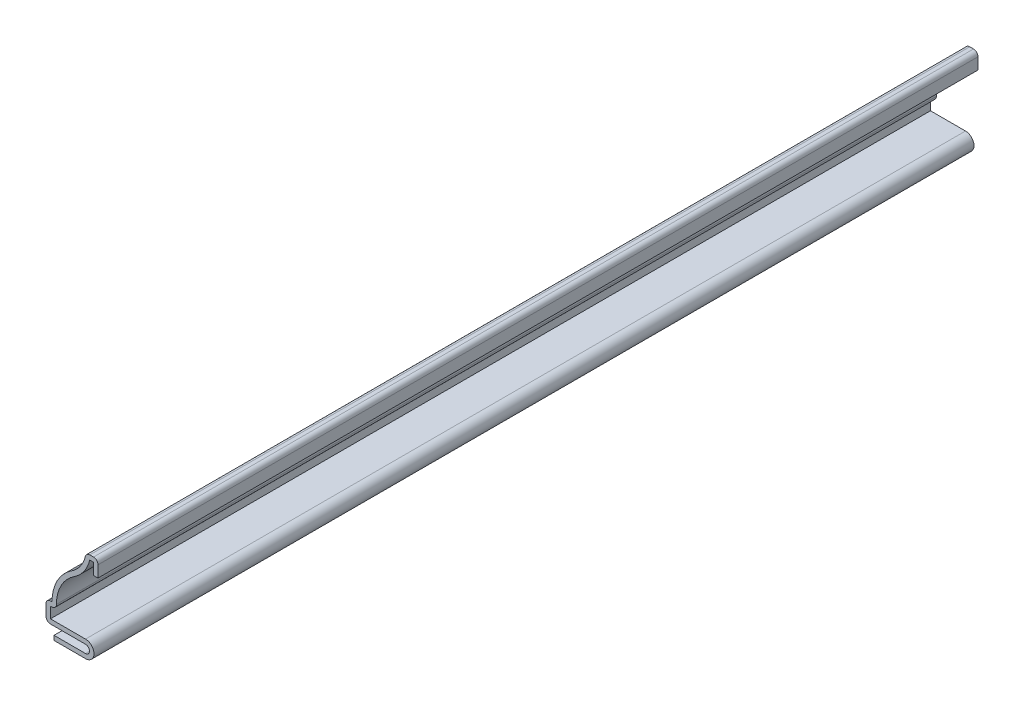
SolidWorks part; units mm, degrees
ref_plane "Front Plane" through (0, 0, 0) normal (0, 0, 1) x (1, 0, 0)
ref_plane "Top Plane" through (0, 0, 0) normal (0, 1, 0) x (1, 0, 0)
ref_plane "Right Plane" through (0, 0, 0) normal (1, 0, 0) x (0, 0, -1)
sketch "Sketch1" plane through (0, 0, 0) normal (0, 0, 1) x (1, 0, 0)
  line L0 (-0.889, 15.0812) -> (-0.889, 17.3672)
  line L1 (-0.889, 17.3672) -> (-1.6407, 17.3672)
  line L2 (-8.1928, 5.5563) -> (-9.4298, 5.5562)
  line L3 (-9.4298, 5.5562) -> (-9.4298, 3.3655)
  line L4 (-9.4298, 3.3655) -> (-2.4765, 3.3655)
  line L5 (-2.4765, 0) -> (-8.7312, 0)
  line L6 (0, 15.0812) -> (0, 18.2562)
  line L7 (0, 18.2562) -> (-2.3812, 18.2562)
  line L8 (-9.1323, 6.4452) -> (-10.3188, 6.4452)
  line L9 (-10.3188, 6.4452) -> (-10.3188, 2.4765)
  line L10 (-10.3188, 2.4765) -> (-2.4765, 2.4765)
  line L11 (-2.4765, 0.889) -> (-8.7312, 0.889)
  line L12 (-0.889, 15.0812) -> (0, 15.0812)
  line L13 (-8.7312, 0) -> (-8.7312, 0.889)
  arc A0 (-1.6407, 17.3672) -> (-4.7069, 12.9997) centre (-8.6814, 19.05) cw
  arc A1 (-4.7069, 12.9997) -> (-8.1928, 5.5563) centre (-0.4011, 6.4452) ccw
  arc A2 (-2.4765, 3.3655) -> (-2.4765, 0) centre (-2.4765, 1.6827) cw
  arc A3 (-2.3812, 18.2562) -> (-5.195, 13.7427) centre (-8.6814, 19.05) cw
  arc A4 (-5.195, 13.7427) -> (-9.1323, 6.4452) centre (-0.4011, 6.4452) ccw
  arc A5 (-2.4765, 2.4765) -> (-2.4765, 0.889) centre (-2.4765, 1.6827) cw
  arc A6 (-1.6407, 17.3672) -> (-4.7069, 12.9997) centre (-8.6814, 19.05) cw construction
  arc A7 (-2.4765, 3.3655) -> (-2.4765, 0) centre (-2.4765, 1.6827) cw construction
  arc A8 (-4.7069, 12.9997) -> (-8.1928, 5.5563) centre (-0.4011, 6.4452) ccw construction
  point P2 (-24.6067, 17.294)
  point P3 (-26.493, 69.5841)
  point P8 (-2.3812, 22.1373)
  point P13 (0, 0)
  point P14 (-35.6752, 54.6797)
  point P30 (-23.8274, 71.2888)
  point P31 (0, 0)
  point P33 (-27.8676, 70.4496)
  point P34 (-31.7876, 70.4496)
  point P35 (-32.6741, 64.6968)
  point P36 (-53.118, 45.977)
  point P37 (-29.3108, 15.2878)
  point P38 (0, 0)
  point P40 (0, 0)
  point P41 (0, 0)
  dimension "D2" = 6.35
  dimension "D3" = 8.7312
  dimension "D11" = 7.9375
  dimension "D12" = 0.7937
  dimension "D4" = 3.9688
  dimension "D5" = 1.5875
  dimension "D6" = 0.7937
  dimension "D7" = 3.175
  dimension "D8" = 2.3813
  dimension "D9" = 11.811
  dimension "D10" = 1.5875
  dimension "D13" = 18.2562
  dimension "D1" = 0.889
extrude "Boss-Extrude1" add sketch "Sketch1" against normal blind 174.625
fillet "Fillet1" radius 0.889 5 edges at (-10.3188, 2.4765, -87.3125) (-10.3188, 6.4452, -87.3125) (-8.1928, 5.5563, -87.3125) (-2.3812, 18.2563, -87.3125) (0, 18.2562, -87.3125)
